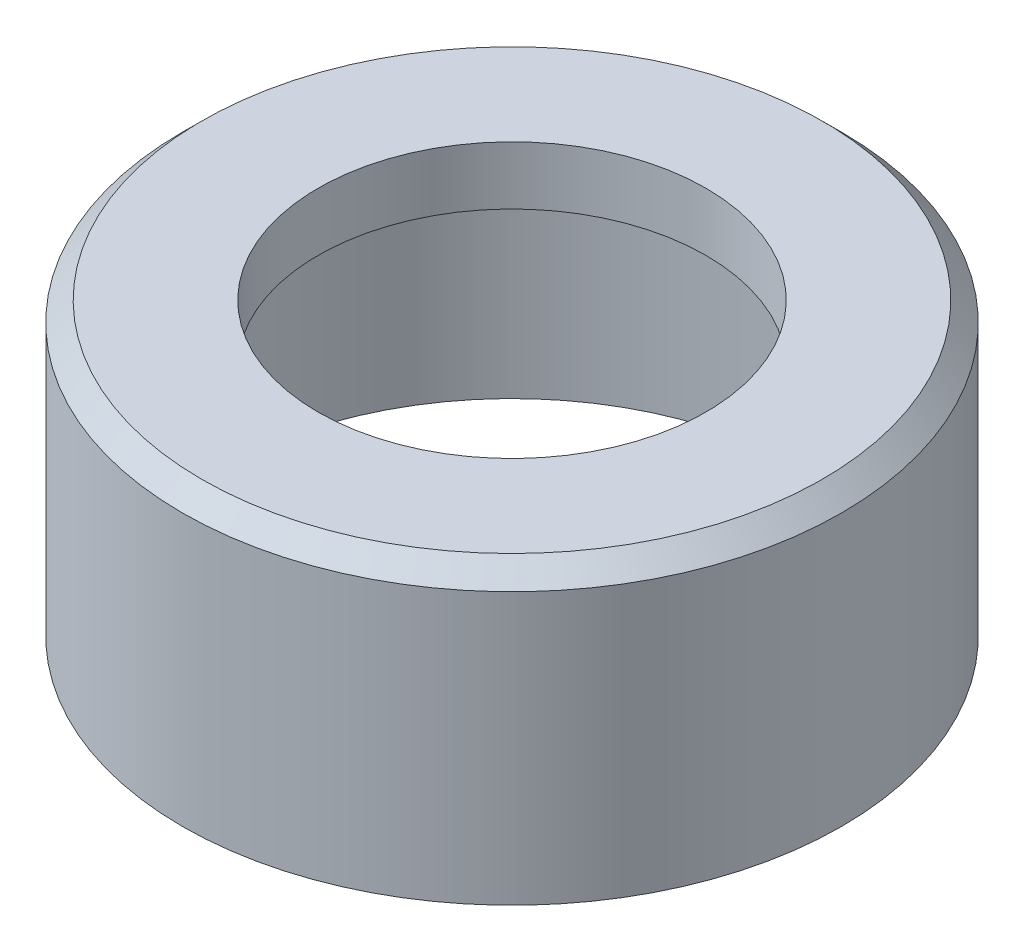
SolidWorks part; units mm, degrees
ref_plane "Front Plane" through (0, 0, 0) normal (0, 0, 1) x (1, 0, 0)
ref_plane "Top Plane" through (0, 0, 0) normal (0, 1, 0) x (1, 0, 0)
ref_plane "Right Plane" through (0, 0, 0) normal (1, 0, 0) x (0, 0, -1)
sketch "Sketch1" plane through (0, 0, 0) normal (0, 1, 0) x (1, 0, 0)
  circle A0 centre (0, 0) radius 8.5
  circle A1 centre (0, 0) radius 7.5
  dimension "D1" = 17
  dimension "D2" = 15
extrude "Boss-Extrude1" add sketch "Sketch1" along normal blind 6
sketch "Sketch3" plane through (0, 6, 0) normal (0, 1, 0) x (1, 0, 0)
  circle A0 centre (0, 0) radius 8.5
  circle A1 centre (0, 0) radius 5
  circle A2 centre (0, 0) radius 8.5 construction
  dimension "D1" = 10
extrude "Boss-Extrude2" add sketch "Sketch3" along normal blind 1.5
chamfer "Chamfer1" distance 0.5 angle 45 1 edges at (0, 7.5, 8.5)
equation "\"D1@Sketch1\"=\"D2@Sketch1\"+2"
